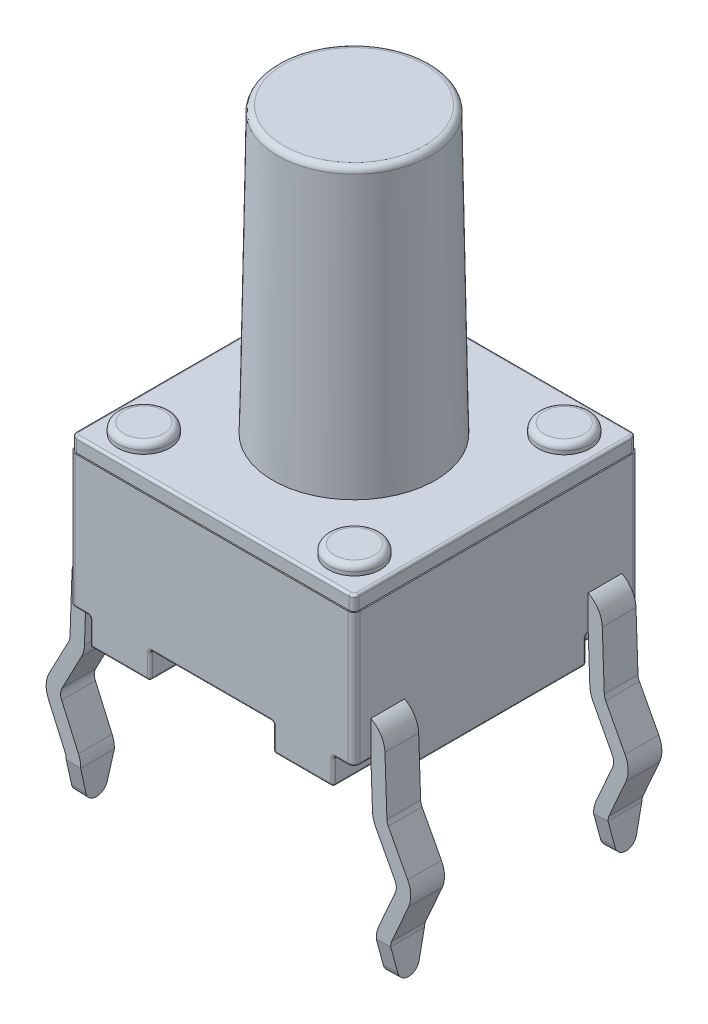
SolidWorks part; units mm, degrees
ref_plane "Front Plane" through (0, 0, 0) normal (0, 0, 1) x (1, 0, 0)
ref_plane "Top Plane" through (0, 0, 0) normal (0, 1, 0) x (1, 0, 0)
ref_plane "Right Plane" through (0, 0, 0) normal (1, 0, 0) x (0, 0, -1)
sketch "Sketch1" plane through (0, 0, 0) normal (0, 1, 0) x (1, 0, 0)
  line L1 (-3.0035, -3.0035) -> (3.0035, -3.0035)
  line L2 (-3.0035, -3.0035) -> (-3.0035, 3.0036)
  line L3 (-3.0035, 3.0036) -> (3.0035, 3.0036)
  line L4 (3.0035, -3.0035) -> (3.0035, 3.0036)
  line L5 (-3.0035, -3.0035) -> (3.0035, 3.0036) construction
  line L6 (-3.0035, 3.0036) -> (3.0035, -3.0035) construction
  point P0 (0, 0)
  dimension "D1" = 6.0071
  dimension "D2" = 6.0071
extrude "Boss-Extrude1" add sketch "Sketch1" along normal blind 2.8194 from offset 0.5588
fillet "Fillet1" radius 0.127 4 edges at (-3.0035, 1.9685, 3.0035) (-3.0035, 1.9685, -3.0036) (3.0035, 1.9685, -3.0036) (3.0035, 1.9685, 3.0035)
sketch "Sketch2" plane through (0, 3.3782, 0) normal (0, -1, 0) x (-1, 0, 0)
  line L8 (2.9781, -2.8765) -> (2.9781, 2.8765)
  line L9 (-2.8765, -2.9781) -> (2.8765, -2.9781)
  line L10 (-2.9781, 2.8765) -> (-2.9781, -2.8765)
  line L11 (2.8765, 2.9782) -> (-2.8765, 2.9782)
  line L12 (2.9781, -2.8765) -> (2.9781, 2.8765)
  line L13 (-2.8765, -2.9781) -> (2.8765, -2.9781)
  line L14 (-2.9781, 2.8765) -> (-2.9781, -2.8765)
  line L15 (2.8765, 2.9782) -> (-2.8765, 2.9782)
  arc A8 (2.8765, -2.9781) -> (2.9781, -2.8765) centre (2.8765, -2.8765) ccw
  arc A9 (-2.9781, -2.8765) -> (-2.8765, -2.9781) centre (-2.8765, -2.8765) ccw
  arc A10 (-2.8765, 2.9782) -> (-2.9781, 2.8765) centre (-2.8765, 2.8766) ccw
  arc A11 (2.9781, 2.8765) -> (2.8765, 2.9782) centre (2.8765, 2.8765) ccw
  arc A12 (2.8765, -2.9781) -> (2.9781, -2.8765) centre (2.8765, -2.8765) ccw
  arc A13 (-2.9781, -2.8765) -> (-2.8765, -2.9781) centre (-2.8765, -2.8765) ccw
  arc A14 (-2.8765, 2.9782) -> (-2.9781, 2.8765) centre (-2.8765, 2.8766) ccw
  arc A15 (2.9781, 2.8765) -> (2.8765, 2.9782) centre (2.8765, 2.8765) ccw
  dimension "D1" = 0.0254
extrude "Boss-Extrude2" add sketch "Sketch2" against normal blind 0.3048
sketch "Sketch3" plane through (0, 0, 0) normal (0, 1, 0) x (1, 0, 0)
  line L0 (-2.5662, -3.0035) -> (-2.5662, -1.8948)
  line L1 (-2.8765, -3.0035) -> (2.8765, -3.0035) construction
  line L2 (-2.5662, -1.8948) -> (-3.0035, -1.8948)
  line L3 (-3.0035, 2.8765) -> (-3.0035, -2.8765) construction
  line L4 (-2.4413, -0.5609) -> (-1.3018, -0.5609)
  line L5 (-1.3018, -0.5609) -> (-1.3017, -3.0035)
  line L6 (-2.4413, -0.5609) -> (-2.4413, 0.5609)
  line L7 (-2.5662, -3.0035) -> (-1.3017, -3.0035)
  line L8 (-3.0035, -1.8948) -> (-3.0035, 1.8948)
  line L9 (-2.4413, 0) -> (-3.0035, 0) construction
  line L10 (-2.5662, 3.0036) -> (-1.3017, 3.0035)
  line L11 (-1.3017, 0.5609) -> (-1.3017, 3.0035)
  line L12 (-2.4413, 0.5609) -> (-1.3017, 0.5609)
  line L13 (-2.5662, 1.8948) -> (-3.0035, 1.8948)
  line L14 (-2.5662, 3.0036) -> (-2.5662, 1.8948)
  line L15 (0, -3.0035) -> (0, 3.0036) construction
  line L16 (2.8765, 3.0036) -> (-2.8765, 3.0036) construction
  line L17 (2.4413, 0) -> (3.0035, 0) construction
  line L18 (2.5662, 3.0035) -> (2.5662, 1.8948)
  line L19 (2.5662, 1.8948) -> (3.0035, 1.8948)
  line L20 (2.4413, 0.5609) -> (1.3017, 0.5609)
  line L21 (1.3017, 0.5609) -> (1.3017, 3.0035)
  line L22 (2.5662, 3.0035) -> (1.3017, 3.0035)
  line L23 (3.0035, -1.8948) -> (3.0035, 1.8948)
  line L24 (2.5662, -3.0036) -> (1.3017, -3.0036)
  line L25 (2.4413, -0.5609) -> (2.4413, 0.5609)
  line L26 (1.3017, -0.5609) -> (1.3017, -3.0036)
  line L27 (2.4413, -0.5609) -> (1.3017, -0.5609)
  line L28 (2.5662, -1.8948) -> (3.0035, -1.8948)
  line L29 (2.5662, -3.0036) -> (2.5662, -1.8948)
  dimension "D1" = 1.7018
extrude "Boss-Extrude3" add sketch "Sketch3" along normal up to next
sketch "Sketch4" plane through (0, 3.683, 0) normal (0, 1, 0) x (1, 0, 0)
  line L1 (-2.2217, -2.2129) -> (2.2217, -2.2129) construction
  line L2 (-2.2217, -2.2129) -> (-2.2217, 2.2129) construction
  line L3 (-2.2217, 2.2129) -> (2.2217, 2.2129) construction
  line L4 (2.2217, -2.2129) -> (2.2217, 2.2129) construction
  line L5 (-2.2217, -2.2129) -> (2.2217, 2.2129) construction
  line L6 (-2.2217, 2.2129) -> (2.2217, -2.2129) construction
  circle A0 centre (2.2217, 2.2129) radius 0.5461
  circle A1 centre (-2.2217, 2.2129) radius 0.5461
  circle A2 centre (-2.2217, -2.2129) radius 0.5461
  circle A3 centre (2.2217, -2.2129) radius 0.5461
  point P0 (0, 0)
  dimension "D1" = 1.0922
extrude "Boss-Extrude4" add sketch "Sketch4" along normal blind 0.2032
sketch "Sketch5" plane through (0, 3.683, 0) normal (0, 1, 0) x (1, 0, 0)
  circle A0 centre (0, 0) radius 1.7145
  dimension "D1" = 3.429
extrude "Boss-Extrude5" add sketch "Sketch5" along normal blind 6 draft 1
fillet "Fillet2" radius 0.127 5 edges at (-2.2217, 3.8862, -1.6668) (-2.2217, 3.8862, 2.759) (2.2217, 3.8862, -1.6668) (2.2217, 3.8862, 2.759) (0, 9.683, 1.6098)
fillet "Fillet3" radius 0.0508 88 edges at (2.9664, 0.5588, 2.9664) (2.9664, 0.5588, -2.9664) (-2.9664, 0.5588, -2.9664) (-2.9664, 0.5588, 2.9664) (3.0035, 0.5588, 2.3857) (3.0035, 0.5588, -2.3857) (1.3017, 0.2794, 3.0036) (1.3017, 0.2794, -3.0035) (2.9484, 3.683, -2.9484) (0, 3.683, -2.9782) (-2.9484, 3.683, -2.9484) (-2.9781, 3.683, 0) (-2.9484, 3.683, 2.9484) (0, 3.683, 2.9781) (2.9484, 3.683, 2.9484) (2.4413, 0.2794, 0.5609) (1.3017, 0.2794, 0.5609) (1.3017, 0.2794, -0.5609) (2.4413, 0.2794, -0.5609) (-1.3018, 0.2794, 0.5609) (-2.4413, 0.2794, 0.5609) (-2.4413, 0.2794, -0.5609) (-1.3017, 0.2794, -0.5609) (2.7849, 0.5588, 1.8948) (3.0035, 0.2794, 1.8948) (2.5662, 0.2794, 3.0036) (2.5662, 0.5588, 2.4492) (2.5662, 0.2794, 1.8948) (3.0035, 0.2794, -1.8948) (2.7849, 0.5588, -1.8948) (2.5662, 0.2794, -1.8948) (2.5662, 0.5588, -2.4492) (2.5662, 0.2794, -3.0035) (-2.5662, 0.2794, -1.8948) (-2.5662, 0.2794, 1.8948) (-1.8715, 0.5588, -0.5609) (-2.4413, 0.5588, 0) (-1.8715, 0.5588, 0.5609) (1.3017, 0.5588, 1.7822) (1.8715, 0.5588, 0.5609) (2.4413, 0.5588, 0) (1.8715, 0.5588, -0.5609) (1.3017, 0.5588, -1.7822) (-1.3017, 0, 1.7822) (-1.8715, 0, 0.5609) (-2.4413, 0, 0) (-1.8715, 0, -0.5609) (-1.3017, 0, -1.7822) (-1.934, 0, -3.0035) (-2.5662, 0, -2.4492) (-2.7849, 0, -1.8948) (-3.0035, 0, 0) (-2.7849, 0, 1.8948) (-2.5662, 0, 2.4492) (-1.934, 0, 3.0035) (1.3017, 0, -1.7822) (1.8715, 0, -0.5609) (2.4413, 0, 0) (1.8715, 0, 0.5609) (1.3017, 0, 1.7822) (1.934, 0, 3.0036) (2.5662, 0, 2.4492) (2.7849, 0, 1.8948) (3.0035, 0, 0) (2.7849, 0, -1.8948) (2.5662, 0, -2.4492) (1.934, 0, -3.0035) (2.9781, 3.683, 0)
sketch "Sketch6" plane through (0, 0, 3.0035) normal (0, 0, 1) x (1, 0, 0)
  line L0 (-2.9873, 1.0641) -> (-3.0423, -0.5107)
  line L1 (-3.0423, -0.5107) -> (-3.5687, -1.5089)
  line L2 (-3.5687, -1.5089) -> (-3.1132, -2.5415)
  line L3 (-3.1132, -2.5415) -> (-3.1424, -3.3782)
  line L4 (-2.9873, 1.0641) -> (-2.5265, 1.0641)
  line L5 (-1.3525, 0) -> (-2.5154, 0) construction
  dimension "D1" = 4.445
  dimension "D2" = 3.3782
  dimension "D3" = 3.0226
  dimension "D4" = 3.5687
  dimension "D5" = 2.032
  dimension "D6" = 1.5748
  dimension "D7" = 92
extrude "Extrude-Thin1" add sketch "Sketch6" against normal blind 0.7112 from offset 0.3556 thin offset against normal yes
sketch "Sketch9" plane through (-3.3254, 0.1161, 0) normal (-0.9994, 0.0349, 0) x (0, 0, 1)
  line L0 (2.6479, -2.7766) -> (2.5175, -3.3091)
  line L1 (2.0672, -3.3091) -> (1.9367, -2.7766)
  line L2 (1.9367, -3.4858) -> (2.6479, -3.4858) construction
  line L3 (2.6479, -2.7766) -> (2.6479, -3.4858)
  line L4 (2.6479, -3.4858) -> (1.9367, -3.4858)
  line L5 (1.9367, -3.4858) -> (1.9367, -2.7766)
  arc A0 (2.5175, -3.3091) -> (2.0672, -3.3091) centre (2.2923, -3.254) cw
  line M1 (2.6479, -3.4858) -> (2.6479, -2.7766)
  line M3 (1.9367, -2.7766) -> (1.9367, -3.4858)
  line M4 (1.9367, -3.4858) -> (2.6479, -3.4858)
extrude "Cut-Extrude1" cut sketch "Sketch9" against normal blind 0.7112 contours L0 A0 L4 M1 | A0 L1 M4 M3
mirror "Mirror1" about plane through (0, 0, 0) normal (0, 0, 1) of "Cut-Extrude1", "Extrude-Thin1"
mirror "Mirror3" about plane through (0, 0, 0) normal (1, 0, 0) of "Mirror1", "Cut-Extrude1", "Extrude-Thin1"
